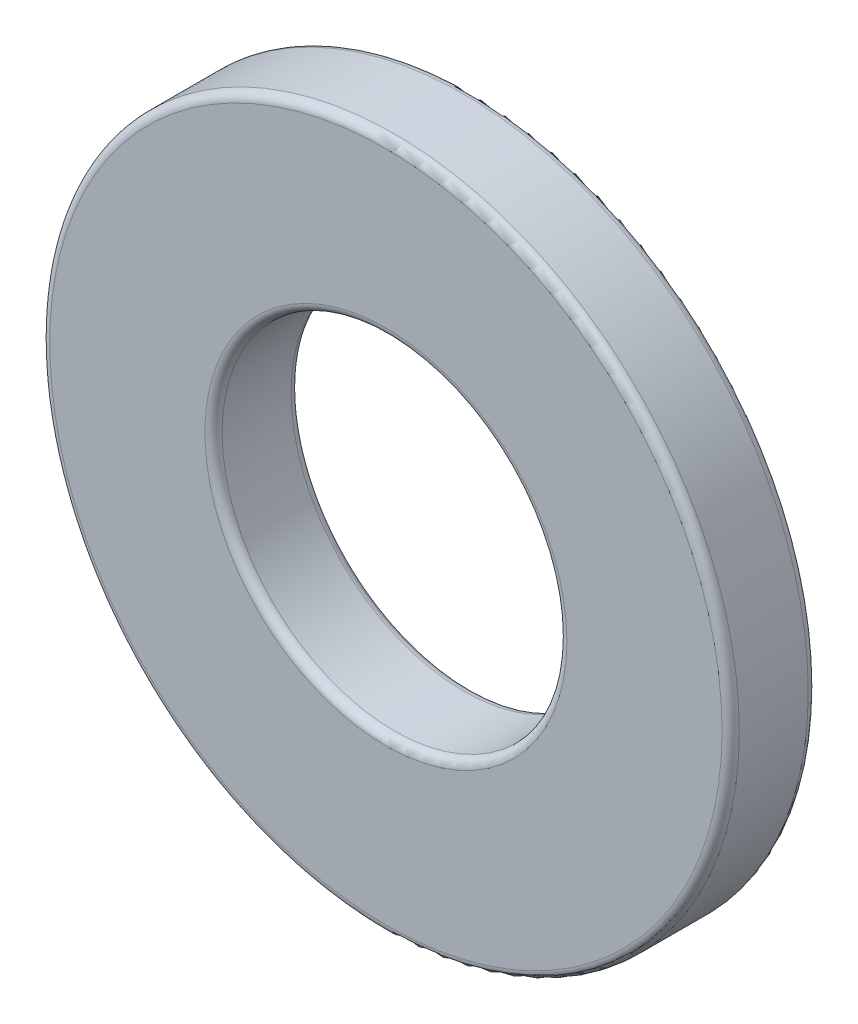
SolidWorks part; units mm, degrees
material "AISI 1020"
ref_plane "Front Plane" through (0, 0, 0) normal (0, 0, 1) x (1, 0, 0)
ref_plane "Top Plane" through (0, 0, 0) normal (0, 1, 0) x (1, 0, 0)
ref_plane "Right Plane" through (0, 0, 0) normal (1, 0, 0) x (0, 0, -1)
sketch "Sketch1" plane through (0, 0, 0) normal (0, 0, 1) x (1, 0, 0)
  line L0 (-6, 0) -> (-3, 0) construction
  line L1 (-3, 0) -> (3, 0) construction
  line L2 (3, 0) -> (6, 0) construction
  line L3 (0, 6) -> (0, -6) construction
  circle A0 centre (0, 0) radius 3 construction
  circle A1 centre (0, 0) radius 6 construction
  dimension "ID" = 6
  dimension "OD" = 12
sketch "Sketch2" plane through (0, 0, 0) normal (1, 0, 0) x (0, 0, -1)
  line L1 (-0.75, -6) -> (0.75, -6) construction
  line L2 (-0.75, -6) -> (-0.75, 6) construction
  line L3 (-0.75, 6) -> (0.75, 6) construction
  line L4 (0.75, -6) -> (0.75, 6) construction
  line L5 (-0.75, -6) -> (0.75, 6) construction
  line L6 (-0.75, 6) -> (0.75, -6) construction
  point P0 (0, 0)
  dimension "Thickness" = 1.5
sketch "Sketch3" plane through (0, 0, 0) normal (0, 0, 1) x (1, 0, 0)
  circle A0 centre (0, 0) radius 3 construction
  circle A1 centre (0, 0) radius 6 construction
  circle A2 centre (0, 0) radius 3
  circle A3 centre (0, 0) radius 6
extrude "Boss-Extrude1" add sketch "Sketch3" along normal up to vertex (0.75 mm away) and the other way up to vertex (0.75 mm away) up to point (0, 6, 0.75) other way up to point (0, 6, -0.75)
fillet "Fillet1" radius 0.15 4 edges at (6, 0, -0.75) (3, 0, -0.75) (3, 0, 0.75) (6, 0, 0.75)
equation "\"D1@Fillet1\"=\"Thickness@Sketch2\"*.1"
